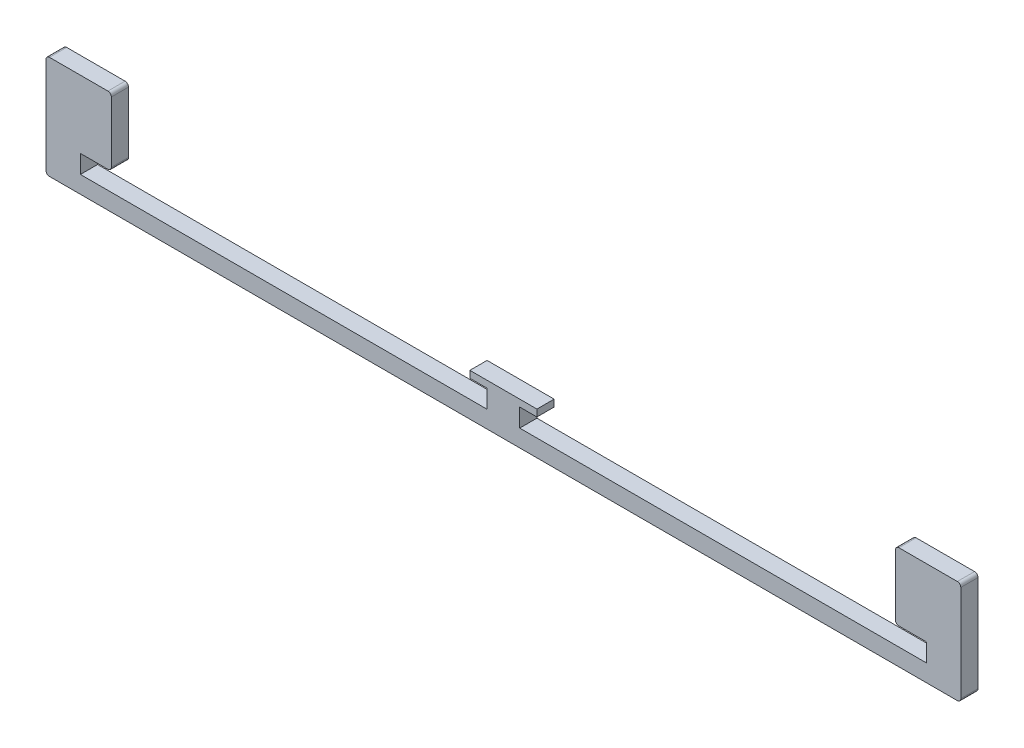
SolidWorks part; units mm, degrees
ref_plane "Front" through (0, 0, 0) normal (0, 0, 1) x (1, 0, 0)
ref_plane "Top" through (0, 0, 0) normal (0, 1, 0) x (1, 0, 0)
ref_plane "Right" through (0, 0, 0) normal (1, 0, 0) x (0, 0, -1)
sketch "Sketch1" plane through (0, 0, 0) normal (0, 0, 1) x (1, 0, 0)
  line L1 (0, 0) -> (133, 0)
  line L3 (10, 5) -> (128.25, 5)
  line L8 (10, 5) -> (10, 10.3)
  line L9 (10, 10.3) -> (19, 10.3)
  line L11 (0, 30) -> (19, 30)
  line L12 (19, 10.3) -> (19, 30)
  line L22 (128.25, 5) -> (128.25, 10.3)
  line L25 (123.25, 10.3) -> (128.25, 10.3)
  line L26 (123.25, 10.3) -> (123.25, 12.3)
  line L27 (123.25, 12.3) -> (133, 12.3)
  line L30 (0, 30) -> (0, 0)
  line L31 (133, 12.3) -> (133, 0)
  dimension "D2" = 5
  dimension "D3" = 5.3
  dimension "D4" = 4.75
  dimension "D5" = 123
  dimension "D8" = 30
  dimension "D9" = 10
  dimension "D10" = 19
  dimension "D14" = 5
  dimension "D15" = 2
  dimension "D16" = 5.3
extrude "Boss-Extrude1" add sketch "Sketch1" along normal blind 5
mirror "Mirror1" about plane through (133, 12.3, 5) normal (-1, 0, 0) of bodies 103
fillet "Fillet1" radius 1 8 edges at (266, 30, 2.5) (266, 0, 2.5) (247, 30, 2.5) (247, 10.3, 2.5) (0, 0, 2.5) (0, 30, 2.5) (19, 30, 2.5) (19, 10.3, 2.5)
